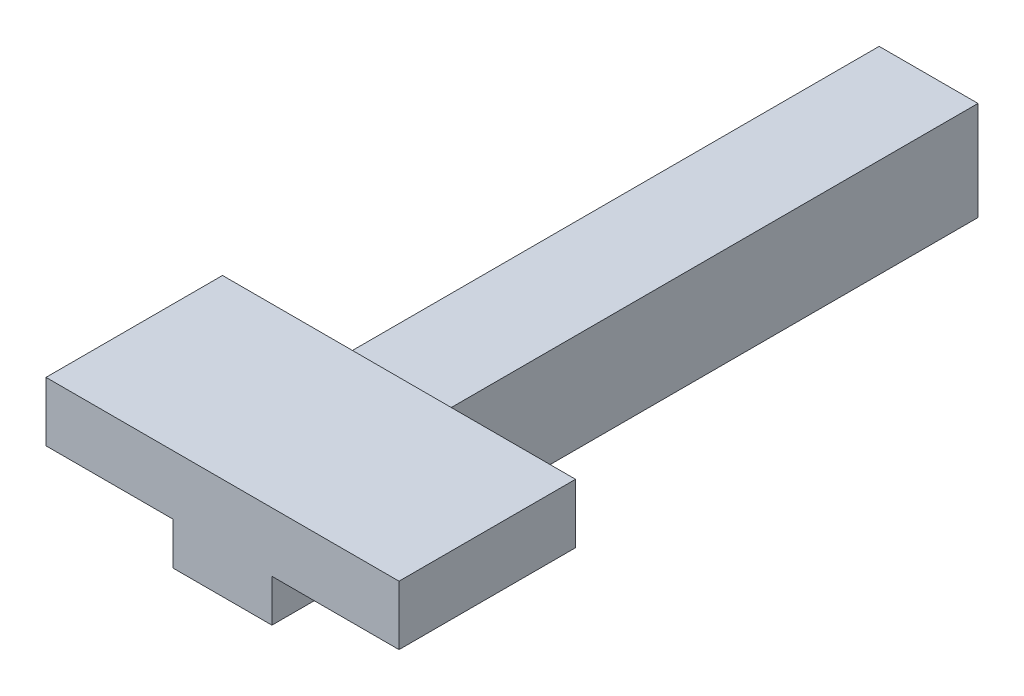
SolidWorks part; units mm, degrees
material "AISI 304"
ref_plane "Front Plane" through (0, 0, 0) normal (0, 0, 1) x (1, 0, 0)
ref_plane "Top Plane" through (0, 0, 0) normal (0, 1, 0) x (1, 0, 0)
ref_plane "Right Plane" through (0, 0, 0) normal (1, 0, 0) x (0, 0, -1)
sketch "Sketch1" plane through (0, 0, 0) normal (0, 0, 1) x (1, 0, 0)
  line L1 (35, 35) -> (-35, 35)
  line L2 (35, 35) -> (35, -35)
  line L3 (35, -35) -> (-35, -35)
  line L4 (-35, 35) -> (-35, -35)
  line L5 (35, 35) -> (-35, -35) construction
  line L6 (35, -35) -> (-35, 35) construction
  point P0 (0, 0)
  dimension "D1" = 70
extrude "Boss-Extrude1" add sketch "Sketch1" along normal blind 500
sketch "Sketch2" plane through (0, 35, 0) normal (0, 1, 0) x (1, 0, 0)
  line L0 (35, -500) -> (-35, -500) construction
  line L1 (-125, -500) -> (125, -500)
  line L2 (-125, -500) -> (-125, -375)
  line L3 (-125, -375) -> (125, -375)
  line L4 (125, -500) -> (125, -375)
  line L5 (-125, -500) -> (125, -375) construction
  line L6 (-125, -375) -> (125, -500) construction
  point P0 (0, -437.5)
  dimension "D1" = 250
  dimension "D2" = 125
extrude "Boss-Extrude2" add sketch "Sketch2" against normal blind 40 and the other way blind 2
